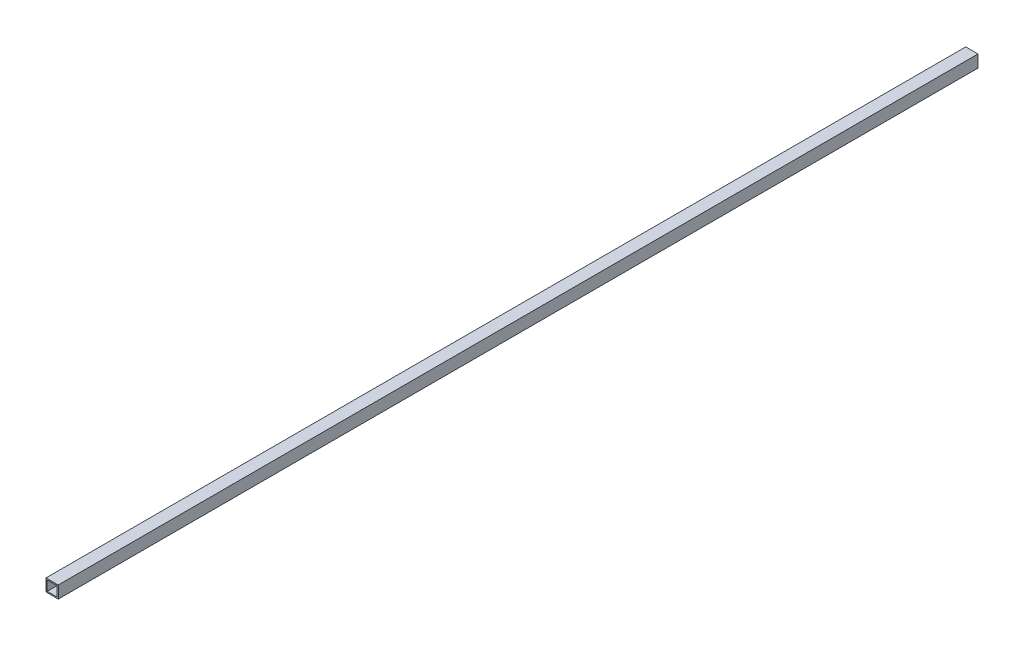
SolidWorks part; units mm, degrees
ref_plane "Front" through (0, 0, 0) normal (0, 0, 1) x (1, 0, 0)
ref_plane "Top" through (0, 0, 0) normal (0, 1, 0) x (1, 0, 0)
ref_plane "Right" through (0, 0, 0) normal (1, 0, 0) x (0, 0, -1)
sketch "Sketch1" plane through (0, 0, 0) normal (0, 0, 1) x (1, 0, 0)
  line L0 (-8, 8) -> (8, 8)
  line L1 (-10, -10) -> (10, -10)
  line L2 (-10, -10) -> (-10, 10)
  line L3 (-10, 10) -> (10, 10)
  line L4 (10, -10) -> (10, 10)
  line L5 (-10, -10) -> (10, 10) construction
  line L6 (-10, 10) -> (10, -10) construction
  line L7 (8, -8) -> (8, 8)
  line L8 (-8, -8) -> (8, -8)
  line L9 (-8, -8) -> (-8, 8)
  point P0 (0, 0)
  dimension "D2" = 20
  dimension "D1" = 2
extrude "Boss-Extrude1" add sketch "Sketch1" along normal blind 1500
